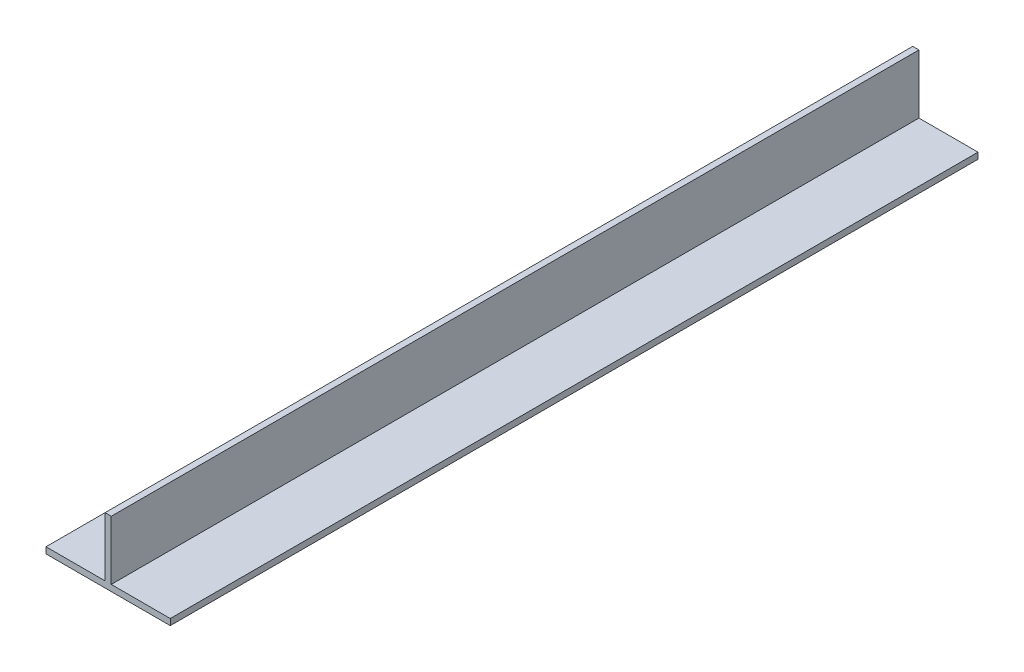
SolidWorks part; units mm, degrees
ref_plane "Alzado" through (0, 0, 0) normal (0, 0, 1) x (1, 0, 0)
ref_plane "Planta" through (0, 0, 0) normal (0, 1, 0) x (1, 0, 0)
ref_plane "Vista lateral" through (0, 0, 0) normal (1, 0, 0) x (0, 0, -1)
sketch "Croquis1" plane through (0, 0, 0) normal (0, 0, 1) x (1, 0, 0)
  line L0 (0, 5.0109) -> (0, -1.6999) construction
  line L1 (-10, 0) -> (-0.5, 0)
  line L2 (-10, 0) -> (-10, -1)
  line L3 (-10, -1) -> (10, -1)
  line L4 (10, 0) -> (10, -1)
  line L5 (-10, 0) -> (10, -1) construction
  line L6 (-10, -1) -> (10, 0) construction
  line L8 (-0.5, 0) -> (-0.5, 9.5)
  line L9 (-0.5, 9.5) -> (0.5, 9.5)
  line L10 (0.5, 0) -> (0.5, 9.5)
  line L11 (0.5, 0) -> (10, 0)
  line L12 (2.26, 0) -> (-2.189, 0) construction
  point P0 (0, -0.5)
  point P12 (0, 9.5)
  dimension "D1" = 1
  dimension "D2" = 1
  dimension "D3" = 20
  dimension "D4" = 9.5
  dimension "D5" = 9.5
extrude "Saliente-Extruir1" add sketch "Croquis1" along normal mid plane 130
